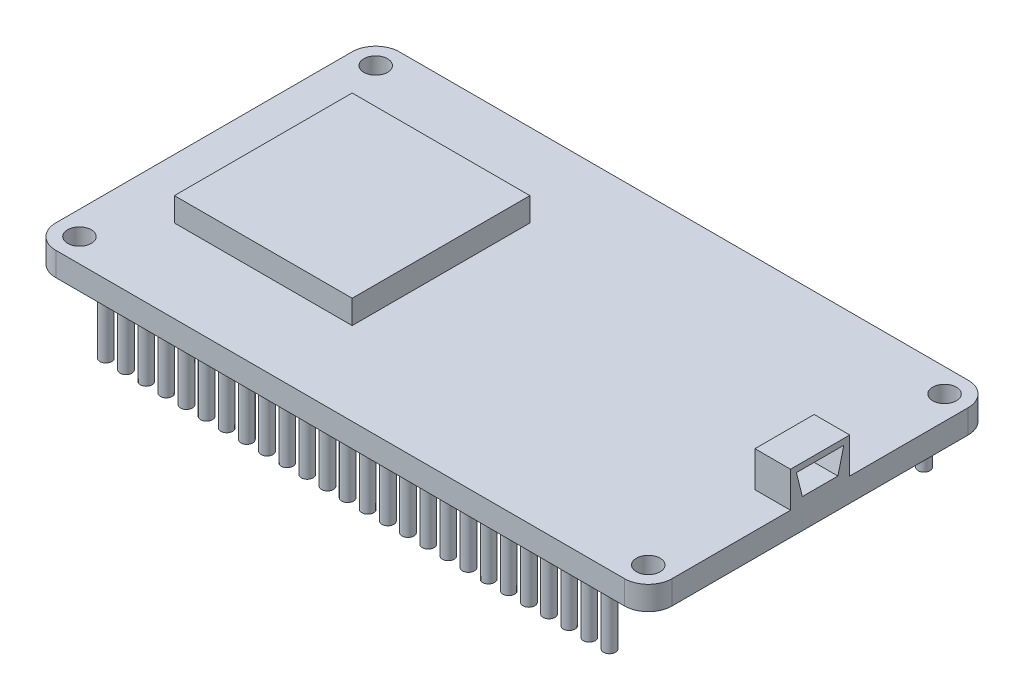
SolidWorks part; units mm, degrees
ref_plane "Plano frontal" through (0, 0, 0) normal (0, 0, 1) x (1, 0, 0)
ref_plane "Plano superior" through (0, 0, 0) normal (0, 1, 0) x (1, 0, 0)
ref_plane "Plano direito" through (0, 0, 0) normal (1, 0, 0) x (0, 0, -1)
sketch "Esboço1" plane through (0, 0, 0) normal (0, 1, 0) x (1, 0, 0)
  line L1 (-25.2765, 12.6305) -> (22.7235, 12.6305)
  line L2 (-27.2765, 10.6305) -> (-27.2765, -14.3695)
  line L3 (-25.2765, -16.3695) -> (22.7235, -16.3695)
  line L4 (24.7235, 10.6305) -> (24.7235, -14.3695)
  arc A0 (22.7235, 12.6305) -> (24.7235, 10.6305) centre (22.7235, 10.6305) cw
  arc A1 (24.7235, -14.3695) -> (22.7235, -16.3695) centre (22.7235, -14.3695) cw
  arc A2 (-25.2765, -16.3695) -> (-27.2765, -14.3695) centre (-25.2765, -14.3695) cw
  arc A3 (-27.2765, 10.6305) -> (-25.2765, 12.6305) centre (-25.2765, 10.6305) cw
  circle A4 centre (-25.2765, 10.6305) radius 1
  circle A5 centre (-25.2765, -14.3695) radius 1
  circle A6 centre (22.7235, 10.6305) radius 1
  circle A7 centre (22.7235, -14.3695) radius 1
  point P6 (24.7235, 12.6305)
  point P11 (-27.2765, -16.3695)
  point P14 (-27.2765, 12.6305)
  dimension "D3" = 2
  dimension "D4" = 2
  dimension "D5" = 2
  dimension "D6" = 2
  dimension "D7" = 2
  dimension "D1" = 52
  dimension "D2" = 29
  dimension "D8" = 48
  dimension "D9" = 25
extrude "Ressalto-extrusão1" add sketch "Esboço1" along normal blind 2
sketch "Esboço2" plane through (0, 0, 0) normal (0, -1, 0) x (1, 0, 0)
  line L0 (-25.2765, 16.3695) -> (22.7235, 16.3695) construction
  line L1 (-27.2765, -10.6305) -> (-27.2765, 14.3695) construction
  line L2 (-27.2765, 1.8695) -> (-25.6655, 1.8695)
  circle A0 centre (-22.2765, 15.1416) radius 0.5
  circle A1 centre (-20.5765, 15.1416) radius 0.5
  circle A2 centre (-18.8765, 15.1416) radius 0.5
  circle A3 centre (-17.1765, 15.1416) radius 0.5
  circle A4 centre (-15.4765, 15.1416) radius 0.5
  circle A5 centre (-13.7765, 15.1416) radius 0.5
  circle A6 centre (-12.0765, 15.1416) radius 0.5
  circle A7 centre (-10.3765, 15.1416) radius 0.5
  circle A8 centre (-8.6765, 15.1416) radius 0.5
  circle A9 centre (-6.9765, 15.1416) radius 0.5
  circle A10 centre (-5.2765, 15.1416) radius 0.5
  circle A11 centre (-3.5765, 15.1416) radius 0.5
  circle A12 centre (-1.8765, 15.1416) radius 0.5
  circle A13 centre (-0.1765, 15.1416) radius 0.5
  circle A14 centre (1.5235, 15.1416) radius 0.5
  circle A15 centre (3.2235, 15.1416) radius 0.5
  circle A16 centre (4.9235, 15.1416) radius 0.5
  circle A17 centre (6.6235, 15.1416) radius 0.5
  circle A18 centre (8.3235, 15.1416) radius 0.5
  circle A19 centre (10.0235, 15.1416) radius 0.5
  circle A20 centre (11.7235, 15.1416) radius 0.5
  circle A21 centre (13.4235, 15.1416) radius 0.5
  circle A22 centre (15.1235, 15.1416) radius 0.5
  circle A23 centre (16.8235, 15.1416) radius 0.5
  circle A24 centre (18.5235, 15.1416) radius 0.5
  circle A25 centre (20.2235, 15.1416) radius 0.5
  circle A26 centre (20.2235, -11.4026) radius 0.5
  circle A27 centre (18.5235, -11.4026) radius 0.5
  circle A28 centre (16.8235, -11.4026) radius 0.5
  circle A29 centre (15.1235, -11.4026) radius 0.5
  circle A30 centre (13.4235, -11.4026) radius 0.5
  circle A31 centre (11.7235, -11.4026) radius 0.5
  circle A32 centre (10.0235, -11.4026) radius 0.5
  circle A33 centre (8.3235, -11.4026) radius 0.5
  circle A34 centre (6.6235, -11.4026) radius 0.5
  circle A35 centre (4.9235, -11.4026) radius 0.5
  circle A36 centre (3.2235, -11.4026) radius 0.5
  circle A37 centre (1.5235, -11.4026) radius 0.5
  circle A38 centre (-0.1765, -11.4026) radius 0.5
  circle A39 centre (-1.8765, -11.4026) radius 0.5
  circle A40 centre (-3.5765, -11.4026) radius 0.5
  circle A41 centre (-5.2765, -11.4026) radius 0.5
  circle A42 centre (-6.9765, -11.4026) radius 0.5
  circle A43 centre (-8.6765, -11.4026) radius 0.5
  circle A44 centre (-10.3765, -11.4026) radius 0.5
  circle A45 centre (-12.0765, -11.4026) radius 0.5
  circle A46 centre (-13.7765, -11.4026) radius 0.5
  circle A47 centre (-15.4765, -11.4026) radius 0.5
  circle A48 centre (-17.1765, -11.4026) radius 0.5
  circle A49 centre (-18.8765, -11.4026) radius 0.5
  circle A50 centre (-20.5765, -11.4026) radius 0.5
  circle A51 centre (-22.2765, -11.4026) radius 0.5
  dimension "D1" = 1
  dimension "D2" = 1.2279
  dimension "D3" = 5
  dimension "D4" = 26
extrude "Ressalto-extrusão2" add sketch "Esboço2" along normal blind 5 contours A0 | A1 | A2 | A3 | A4 | A5 | A6 | A7 | A8 | A9 | A10 | A11 | A12 | A13 | A14 | A15 | A16 | A17 | A18 | A19 | A20 | A21 | A22 | A23 | A24 | A25 | A51 | A50 | A49 | A48 | A47 | A46 | A45 | A44 | A43 | A42 | A41 | A40 | A39 | A38 | A37 | A36 | A35 | A34 | A33 | A32 | A31 | A30 | A29 | A28 | A27 | A26
sketch "Esboço3" plane through (0, 2, 0) normal (0, 1, 0) x (1, 0, 0)
  line L0 (24.7235, -14.3695) -> (24.7235, 10.6305) construction
  line L1 (24.7235, -4.3695) -> (21.7235, -4.3695)
  line L2 (24.7235, -4.3695) -> (24.7235, 0.6305)
  line L3 (24.7235, 0.6305) -> (21.7235, 0.6305)
  line L4 (21.7235, -4.3695) -> (21.7235, 0.6305)
  line L5 (22.7235, 12.6305) -> (-25.2765, 12.6305) construction
  line L6 (-25.2765, -16.3695) -> (22.7235, -16.3695) construction
  dimension "D1" = 5
  dimension "D2" = 3
  dimension "D3" = 12
  dimension "D4" = 12
extrude "Ressalto-extrusão3" add sketch "Esboço3" along normal blind 3
sketch "Esboço4" plane through (24.7235, 0, 0) normal (1, 0, 0) x (0, 0, -1)
  line L0 (-3.3695, 2.5) -> (-0.3695, 2.5)
  line L1 (-3.8695, 4.5) -> (0.1305, 4.5)
  line L3 (-3.3695, 2.5) -> (-0.3695, 2.5)
  line L6 (-4.3695, 5) -> (0.6305, 5) construction
  line L7 (0.6305, 2) -> (10.6305, 2) construction
  line L8 (-3.8695, 4.5) -> (-3.3695, 2.5)
  line L9 (0.1305, 4.5) -> (-0.3695, 2.5)
  dimension "D1" = 4
  dimension "D3" = 0.5
  dimension "D4" = 0.5
  dimension "D6" = 3
extrude "Corte-extrusão1" cut sketch "Esboço4" against normal blind 2 contours L9 L1 L8 L0
sketch "Esboço5" plane through (0, 2, 0) normal (0, 1, 0) x (1, 0, 0)
  line L0 (22.7235, 12.6305) -> (-25.2765, 12.6305) construction
  line L1 (-22.2643, -9.3695) -> (-7.2643, -9.3695)
  line L2 (-22.2643, -9.3695) -> (-22.2643, 5.6305)
  line L3 (-22.2643, 5.6305) -> (-7.2643, 5.6305)
  line L4 (-7.2643, -9.3695) -> (-7.2643, 5.6305)
  line L5 (-25.2765, -16.3695) -> (22.7235, -16.3695) construction
  dimension "D1" = 15
  dimension "D2" = 15
  dimension "D3" = 7
  dimension "D4" = 7
extrude "Ressalto-extrusão4" add sketch "Esboço5" along normal blind 2
